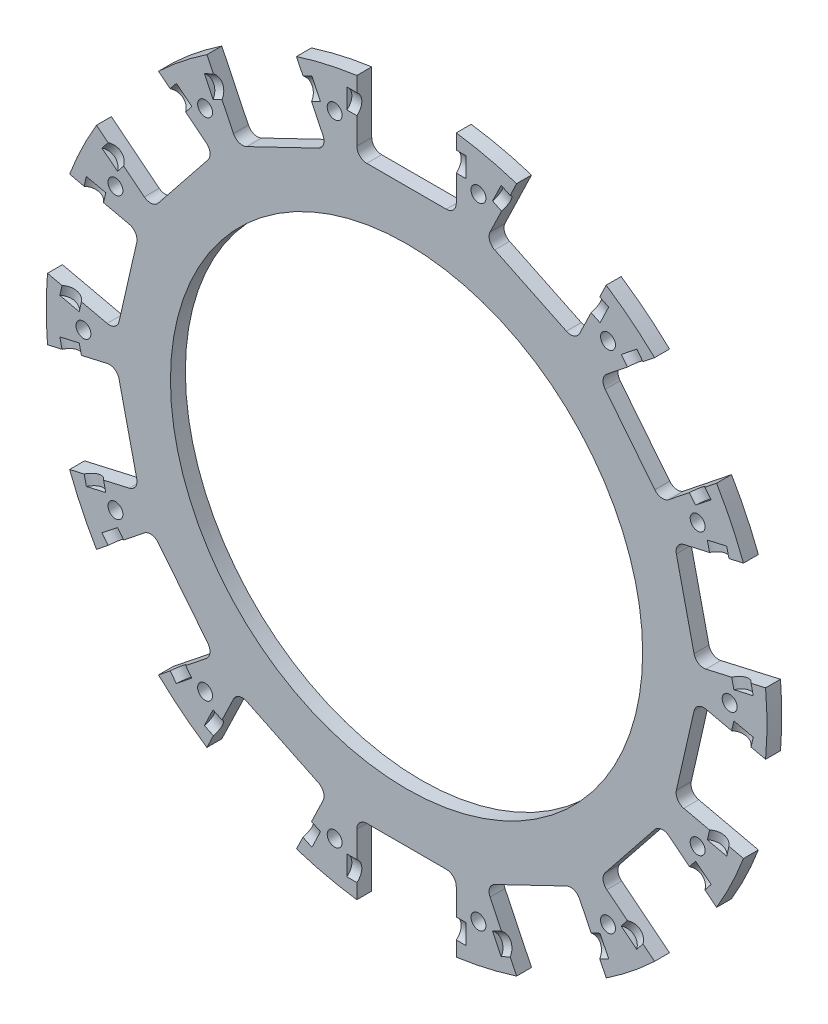
SolidWorks part; units mm, degrees
material "1060 合金"
ref_plane "前视基准面" through (0, 0, 0) normal (0, 0, 1) x (1, 0, 0)
ref_plane "上视基准面" through (0, 0, 0) normal (0, 1, 0) x (1, 0, 0)
ref_plane "右视基准面" through (0, 0, 0) normal (1, 0, 0) x (0, 0, -1)
sketch "草图1" plane through (0, 0, 0) normal (0, 0, 1) x (1, 0, 0)
  circle A0 centre (0, 0) radius 47.5
  dimension "D1" = 95
extrude "凸台-拉伸1" add sketch "草图1" along normal blind 3
sketch "草图2" plane through (0, 0, 3) normal (0, 0, 1) x (1, 0, 0)
  circle A0 centre (0, 0) radius 35 construction
  circle A1 centre (0, 35) radius 11
  dimension "D1" = 70
  dimension "D2" = 22
extrude "切除-拉伸1" cut sketch "草图2" against normal through all
sketch "草图3" plane through (0, 0, 3) normal (0, 0, 1) x (1, 0, 0)
  line L0 (0, 0) -> (11.25, 19.4856) construction
  line L1 (0, -29.6117) -> (0, 46) construction
  circle A0 centre (0, 0) radius 22.5 construction
  circle A1 centre (0, 35) radius 11 construction
  circle A2 centre (11.25, 19.4856) radius 2.55
  dimension "D1" = 45
  dimension "D3" = 5.1
  dimension "D2" = 30
pattern_circular "阵列(圆周)1" count 6 over 360 about axis through (0, 0, 0) along (0, 0, 1) of "切除-拉伸1"
extrude "切除-拉伸2" cut sketch "草图3" against normal through all
pattern_circular "阵列(圆周)2" count 6 over 360 about axis through (0, 0, 0) along (0, 0, 1) of "切除-拉伸2"
sketch "草图4" plane through (0, 0, 3) normal (0, 0, 1) x (1, 0, 0)
  circle A0 centre (0, 0) radius 12.9
  dimension "D1" = 25.8
extrude "切除-拉伸3" cut sketch "草图4" against normal through all
sketch "草图5" plane through (0, 0, 3) normal (0, 0, 1) x (1, 0, 0)
  circle A0 centre (0, 0) radius 72.5
  circle A1 centre (0, 0) radius 47.5
  dimension "D1" = 145
extrude "凸台-拉伸2" add sketch "草图5" against normal blind 3
sketch "草图6" plane through (0, 0, 0) normal (0, 0, -1) x (-1, 0, 0)
  line L0 (0, 0) -> (0, 72.5) construction
  line L1 (-10, 87.5) -> (10, 87.5)
  line L2 (-10, 87.5) -> (-10, 57.5)
  line L3 (-10, 57.5) -> (10, 57.5)
  line L4 (10, 87.5) -> (10, 57.5)
  line L5 (-10, 87.5) -> (10, 57.5) construction
  line L6 (-10, 57.5) -> (10, 87.5) construction
  circle A0 centre (0, 0) radius 72.5 construction
  point P0 (0, 72.5)
  dimension "D1" = 20
  dimension "D2" = 30
extrude "切除-拉伸4" cut sketch "草图6" against normal through all
pattern_circular "阵列(圆周)3" count 14 over 360 about axis through (0, 0, 0) along (0, 0, 1) of "切除-拉伸4"
sketch "草图7" plane through (0, 0, 3) normal (0, 0, 1) x (1, 0, 0)
  line L0 (0, 0) -> (-16.1328, 70.6823) construction
  circle A0 centre (0, 0) radius 65 construction
  arc A1 (-10, 71.807) -> (-22.1462, 69.0347) centre (0, 0) ccw construction
  circle A2 centre (-14.4639, 63.3703) radius 1.5
  dimension "D1" = 130
  dimension "D2" = 3
extrude "切除-拉伸5" cut sketch "草图7" against normal through all
pattern_circular "阵列(圆周)4" count 14 over 360 about axis through (0, 0, 0) along (0, 0, 1) of "切除-拉伸5"
sketch "草图8" plane through (0, 0, 3) normal (0, 0, 1) x (1, 0, 0)
  circle A0 centre (0, 0) radius 47.5
  dimension "D1" = 95
extrude "切除-拉伸6" cut sketch "草图8" against normal through all
sketch "草图9" plane through (-6.2349, 7.8183, 0) normal (0.6235, -0.7818, 0) x (0.7818, 0.6235, 0)
  line L0 (71.807, 1.5) -> (60.3571, 1.5) construction
  line L1 (71.807, 3) -> (71.807, 0) construction
  line L2 (60.3571, 1.5) -> (60.3571, 4.5) construction
  line L3 (60.3571, 4.5) -> (71.807, 4.5) construction
  line L4 (71.807, 4.5) -> (71.807, 1.5) construction
  line L5 (71.807, 1.5) -> (71.807, -1.5) construction
  line L6 (71.807, -1.5) -> (60.3571, -1.5) construction
  line L7 (60.3571, -1.5) -> (60.3571, 1.5) construction
  circle A0 centre (66.807, 4.5) radius 2.5
  dimension "D4" = 5
  dimension "D1" = 3
  dimension "D2" = 3
  dimension "D3" = 11.45
  dimension "D6" = 5
extrude "切除-拉伸7" cut sketch "草图9" against normal blind 2
sketch "草图10" plane through (9.0097, -4.3388, 0) normal (-0.901, 0.4339, 0) x (0, 0, 1)
  line L0 (1.5, 71.807) -> (1.5, 60.3571) construction
  line L1 (0, 71.807) -> (3, 71.807) construction
  line L2 (0, 60.3571) -> (3, 60.3571) construction
  line L3 (1.5, 60.3571) -> (4.5, 60.3571) construction
  line L4 (4.5, 60.3571) -> (4.5, 71.807) construction
  line L5 (4.5, 71.807) -> (1.5, 71.807) construction
  circle A0 centre (4.5, 66.807) radius 2.5
  dimension "D2" = 5
  dimension "D1" = 3
  dimension "D3" = 5
extrude "切除-拉伸8" cut sketch "草图10" against normal blind 2
pattern_circular "阵列(圆周)5" count 14 over 360 about axis through (0, 0, 0) along (0, 0, 1) of "切除-拉伸8", "切除-拉伸7"
fillet "圆角1" radius 2 28 edges at (-15.9386, 56.1445, 1.5) (-38.7204, 43.669, 1.5) (-33.958, 47.4669, 1.5) (-53.8331, 22.5442, 1.5) (-51.1902, 28.0323, 1.5) (-58.2836, 3.0457, 1.5) (-58.2836, -3.0457, 1.5) (-51.1902, -28.0323, 1.5) (-53.8331, -22.5442, 1.5) (-38.7204, -43.669, 1.5) (-33.958, -47.4669, 1.5) (-15.9386, -56.1445, 1.5) (-10, -57.5, 1.5) (10, -57.5, 1.5) (15.9386, -56.1445, 1.5) (33.958, -47.4669, 1.5) (38.7204, -43.669, 1.5) (51.1902, -28.0323, 1.5) (53.8331, -22.5442, 1.5) (58.2836, -3.0457, 1.5) (58.2836, 3.0457, 1.5) (53.8331, 22.5442, 1.5) (51.1902, 28.0323, 1.5) (38.7204, 43.669, 1.5) (33.958, 47.4669, 1.5) (15.9386, 56.1445, 1.5) (10, 57.5, 1.5) (-10, 57.5, 1.5)
